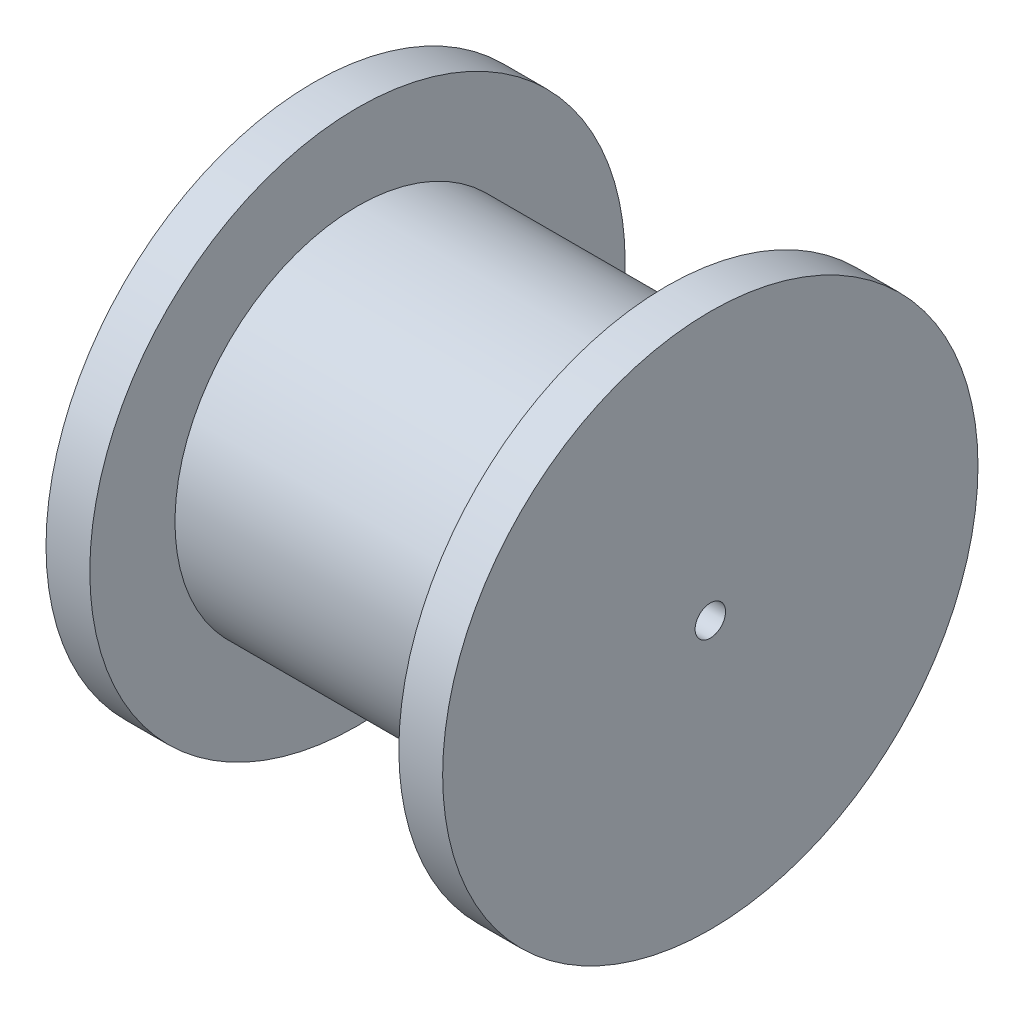
SolidWorks part; units mm, degrees
ref_plane "Front Plane" through (0, 0, 0) normal (0, 0, 1) x (1, 0, 0)
ref_plane "Top Plane" through (0, 0, 0) normal (0, 1, 0) x (1, 0, 0)
ref_plane "Right Plane" through (0, 0, 0) normal (1, 0, 0) x (0, 0, -1)
sketch "Sketch1" plane through (0, 0, 0) normal (0, 0, 1) x (1, 0, 0)
  line L0 (0, 15) -> (-32.6, 15)
  line L1 (0, 0) -> (-32.6, 0)
  line L2 (0, 0) -> (0, 15)
  line L4 (-32.6, 0) -> (-32.6, 15)
  line L6 (-32.6, 15) -> (0, 15)
  line L7 (-32.6, 15) -> (-32.6, 22)
  line L8 (-32.6, 22) -> (0, 22)
  line L9 (0, 15) -> (0, 22)
  line L10 (-29, 22) -> (-29, 15)
  line L11 (-16.3, 22) -> (-16.3, 15) construction
  line L12 (-3.6, 22) -> (-3.6, 15)
  dimension "D1" = 15
  dimension "D2" = 25.4
  dimension "D3" = 7
  dimension "D4" = 3.6
revolve "Revolve1" add sketch "Sketch1" angle 360 about L1
sketch "Sketch2" plane through (-32.6, 0, 0) normal (-1, 0, 0) x (0, 0, 1)
  circle A0 centre (0, 0) radius 1.25
  dimension "D1" = 2.5
extrude "Cut-Extrude1" cut sketch "Sketch2" against normal through all
sketch "Sketch3" [suppressed] plane through (0, 0, 0) normal (1, 0, 0) x (0, 0, -1)
  circle A0 centre (0, 0) radius 22
  circle A1 centre (0, 0) radius 22 construction
extrude "Cut-Extrude2" [suppressed] cut sketch "Sketch3" against normal up to surface (54.4 mm away)
